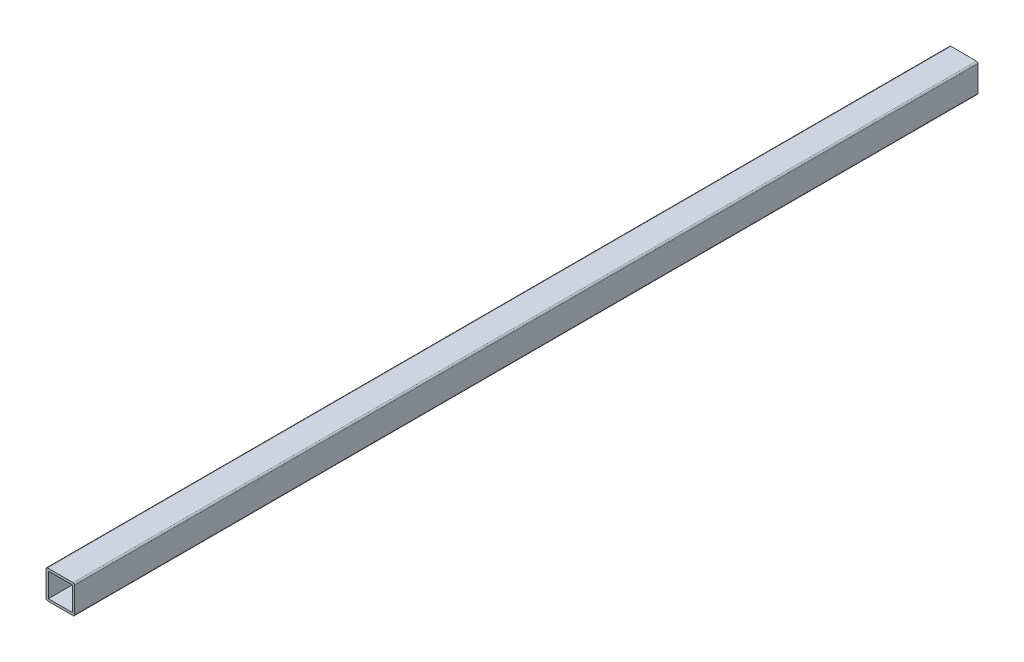
SolidWorks part; units mm, degrees
ref_plane "정면" through (0, 0, 0) normal (0, 0, 1) x (1, 0, 0)
ref_plane "윗면" through (0, 0, 0) normal (0, 1, 0) x (1, 0, 0)
ref_plane "우측면" through (0, 0, 0) normal (1, 0, 0) x (0, 0, -1)
sketch "스케치1" plane through (0, 0, 0) normal (0, 0, 1) x (1, 0, 0)
  line L1 (0, 0) -> (19, 0)
  line L2 (0, 0) -> (0, -19)
  line L3 (0, -19) -> (19, -19)
  line L4 (19, 0) -> (19, -19)
  line L5 (1.56, -1.56) -> (17.44, -1.56)
  line L6 (1.56, -1.56) -> (1.56, -17.44)
  line L7 (1.56, -17.44) -> (17.44, -17.44)
  line L8 (17.44, -1.56) -> (17.44, -17.44)
  dimension "D1" = 19
  dimension "D2" = 19
  dimension "D3" = 15.88
  dimension "D4" = 15.88
  dimension "D5" = 1.56
  dimension "D6" = 1.56
extrude "보스-돌출1" add sketch "스케치1" along normal blind 600
fillet "필렛2" radius 1 4 edges at (0, -19, 300) (0, 0, 300) (19, -19, 300) (19, 0, 300)
